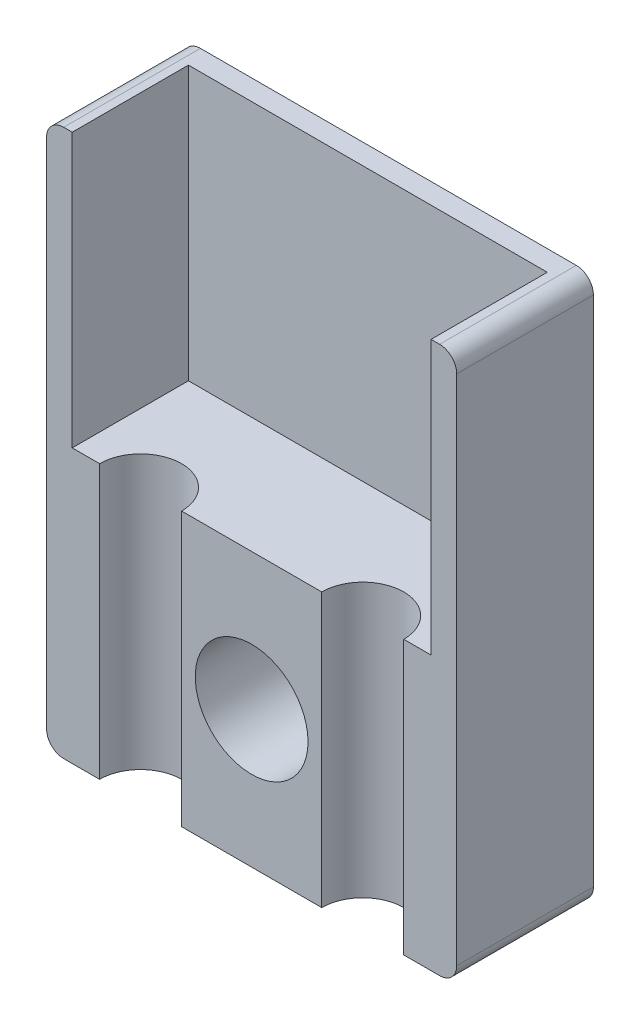
SolidWorks part; units mm, degrees
ref_plane "Front Plane" through (0, 0, 0) normal (0, 0, 1) x (1, 0, 0)
ref_plane "Top Plane" through (0, 0, 0) normal (0, 1, 0) x (1, 0, 0)
ref_plane "Right Plane" through (0, 0, 0) normal (1, 0, 0) x (0, 0, -1)
sketch "Sketch1" plane through (0, 0, 0) normal (0, 0, 1) x (1, 0, 0)
  line L1 (0.5, 0) -> (11.5, 0)
  line L2 (0, 0.5) -> (0, 15.5)
  line L3 (0.5, 16) -> (11.5, 16)
  line L4 (12, 0.5) -> (12, 15.5)
  circle A0 centre (6, 4) radius 1.65
  arc A1 (11.5, 16) -> (12, 15.5) centre (11.5, 15.5) cw
  arc A2 (11.5, 0) -> (12, 0.5) centre (11.5, 0.5) ccw
  arc A3 (0.5, 0) -> (0, 0.5) centre (0.5, 0.5) cw
  arc A4 (0, 15.5) -> (0.5, 16) centre (0.5, 15.5) cw
  point P13 (0, 0)
extrude "Boss-Extrude1" add sketch "Sketch1" along normal blind 4
sketch "Sketch2" plane through (0, 0, 0) normal (0, -1, 0) x (1, 0, 0)
  line L0 (1.55, 4) -> (3.95, 4)
  line L2 (8.05, 4) -> (10.45, 4)
  arc A0 (1.55, 4) -> (3.95, 4) centre (2.75, 4) ccw
  arc A2 (8.05, 4) -> (10.45, 4) centre (9.25, 4) ccw
extrude "Cut-Extrude1" cut sketch "Sketch2" against normal up to surface (16 mm away) up to face at (6, 16, 2)
sketch "Sketch3" plane through (0, 16, 0) normal (0, 1, 0) x (1, 0, 0)
  line L1 (11.5, -4) -> (10.45, -4) construction
  line L3 (1.55, -4) -> (0.5, -4) construction
  line L7 (11.25, -4) -> (0.75, -4)
  line L8 (11.25, -4) -> (11.25, -0.6)
  line L9 (11.25, -0.6) -> (0.75, -0.6)
  line L10 (0.75, -4) -> (0.75, -0.6)
extrude "Cut-Extrude2" cut sketch "Sketch3" against normal offset from surface (8 mm away) 8 up to face at (6, 0, 2.7)
